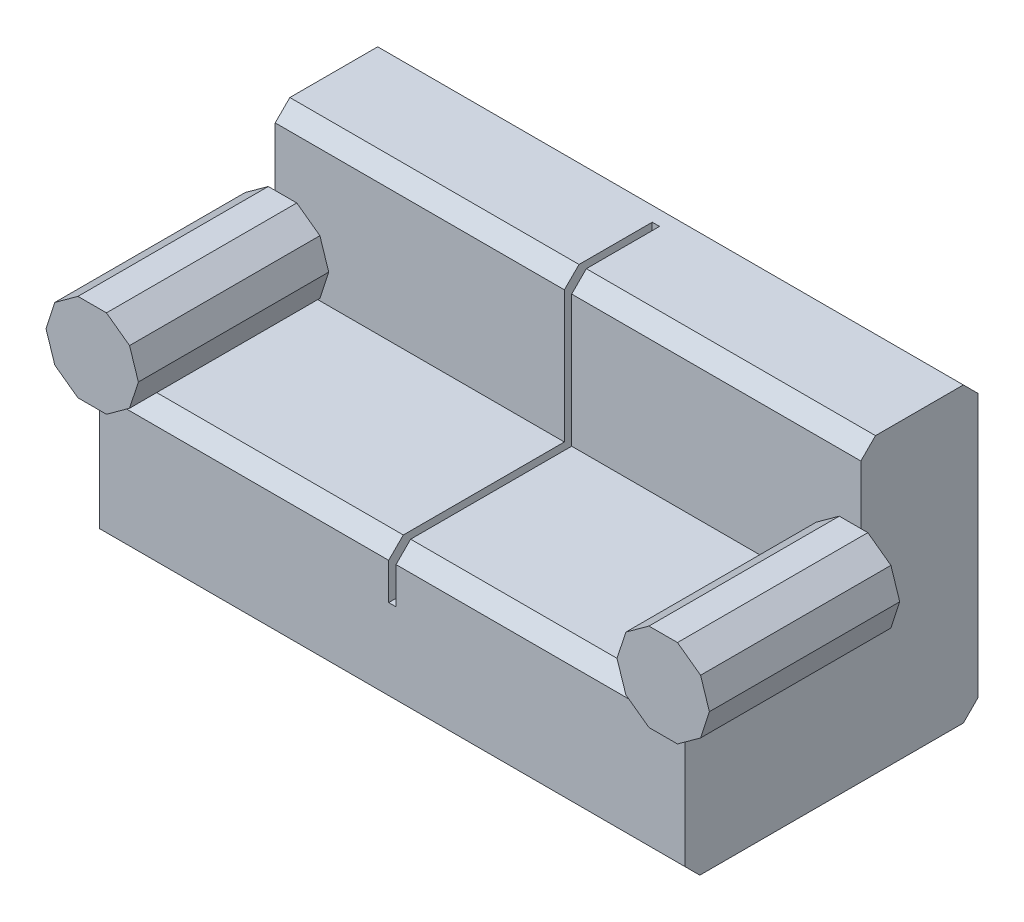
SolidWorks part; units mm, degrees
ref_plane "Front Plane" through (0, 0, 0) normal (0, 0, 1) x (1, 0, 0)
ref_plane "Top Plane" through (0, 0, 0) normal (0, 1, 0) x (1, 0, 0)
ref_plane "Right Plane" through (0, 0, 0) normal (1, 0, 0) x (0, 0, -1)
sketch "Sketch1" plane through (0, 0, 0) normal (1, 0, 0) x (0, 0, -1)
  line L0 (0, 0) -> (-55, 0)
  line L1 (-60, -5) -> (-60, -45)
  line L2 (-55, -50) -> (35, -50)
  line L3 (40, -45) -> (40, 45)
  line L4 (35, 50) -> (5, 50)
  line L5 (0, 45) -> (0, 0)
  line L6 (-55, 0) -> (-60, -5)
  line L7 (5, 50) -> (0, 45)
  line L8 (40, 45) -> (35, 50)
  line L9 (-60, -45) -> (-55, -50)
  line L10 (35, -50) -> (40, -45)
  point P1 (-60, 0)
  point P3 (-60, -50)
  point P4 (40, -50)
  point P5 (40, 50)
  point P6 (0, 50)
  point P17 (40, 0)
  dimension "D1" = 100
  dimension "D2" = 100
  dimension "D8" = 30
extrude "Boss-Extrude1" add sketch "Sketch1" along normal mid plane 200
sketch "Sketch2" plane through (0, 0, 0) normal (0, 0, 1) x (1, 0, 0)
  line L0 (100, 45) -> (100, 0) construction
  line L1 (113.2719, 10) -> (110.2598, 19.2705)
  line L2 (110.2598, 19.2705) -> (102.3738, 25)
  line L3 (102.3738, 25) -> (92.6262, 25)
  line L4 (92.6262, 25) -> (84.7402, 19.2705)
  line L5 (84.7402, 19.2705) -> (81.7281, 10)
  line L6 (81.7281, 10) -> (84.7402, 0.7295)
  line L7 (84.7402, 0.7295) -> (92.6262, -5)
  line L8 (92.6262, -5) -> (102.3738, -5)
  line L9 (102.3738, -5) -> (110.2598, 0.7295)
  line L10 (110.2598, 0.7295) -> (113.2719, 10)
  circle A0 centre (97.5, 10) radius 15 construction
  point P1 (88.7693, 5.2217)
  point P16 (90, 10)
  point P17 (0, 0)
  line M2 (-100, 0) -> (100, 0)
  line M3 (100, 0) -> (100, 45)
  dimension "D2" = 30
  dimension "D1" = 2.5
  dimension "D3" = 10
extrude "Boss-Extrude3" add sketch "Sketch2" along normal offset from surface (65 mm away) 5 contours L5 L6 L2 L3 L4 M2 M3 | L9 L10 L1 L2 L6 L7 L8 M3 M2 up to face at (0, -25, 60) offset beyond the face yes
mirror "Mirror1" about plane through (0, 0, 0) normal (1, 0, 0) of "Boss-Extrude3"
sketch "Sketch5" plane through (0, 0, 0) normal (0, 0, 1) x (1, 0, 0)
  line L0 (-1.25, 0) -> (-1.25, 50)
  line L1 (85.7443, 0) -> (-85.7443, 0) construction
  line L2 (100, 50) -> (-100, 50) construction
  line L3 (-1.25, 50) -> (1.25, 50)
  line L4 (1.25, 50) -> (1.25, 0)
  line L5 (1.25, 0) -> (-1.25, 0)
  point P7 (0, 50)
  dimension "D1" = 2.5
extrude "Cut-Extrude1" cut sketch "Sketch5" against normal blind 10
sketch "Sketch6" plane through (0, 50, 0) normal (0, 1, 0) x (1, 0, 0)
  line L0 (1.25, -60) -> (-1.25, -60)
  line L1 (-1.25, -60) -> (-1.25, 30)
  line L3 (1.25, 30) -> (1.25, -60)
  line L5 (1.25, 10) -> (1.25, 0) construction
  line L6 (92.6262, -60) -> (-92.6262, -60) construction
  line L7 (-1.25, 10) -> (-1.25, 5) construction
  line L8 (-1.25, 30) -> (1.25, 30)
  line L9 (100, 35) -> (-100, 35) construction
  point P3 (0, 30.5593)
  point P8 (0, 0)
  point P13 (0, 0)
  point P14 (0, 0)
  dimension "D1" = 5
extrude "Cut-Extrude3" cut sketch "Sketch6" against normal blind 5
sketch "Sketch7" plane through (0, 0, 0) normal (0, 1, 0) x (1, 0, 0)
  line L0 (-1.25, 10) -> (-1.25, -60)
  line L1 (92.6262, -60) -> (-92.6262, -60) construction
  line L2 (-1.25, -60) -> (1.25, -60)
  line L3 (1.25, -60) -> (1.25, 10)
  line L4 (1.25, 10) -> (-1.25, 10)
extrude "Cut-Extrude4" cut sketch "Sketch7" against normal blind 10
sketch "Sketch8" plane through (0, 0, 60) normal (0, 0, 1) x (1, 0, 0)
  line L0 (-1.25, 0) -> (-1.25, -17.5)
  line L1 (-1.25, 0) -> (-85.7443, 0) construction
  line L2 (-1.25, -5) -> (-1.25, 0) construction
  line L3 (-1.25, -17.5) -> (1.25, -17.5)
  line L4 (1.25, -17.5) -> (1.25, 0)
  line L5 (85.7443, 0) -> (1.25, 0) construction
  line L6 (1.25, 0) -> (-1.25, 0)
  line L7 (1.25, -10) -> (1.25, 45) construction
  line L8 (1.25, -10) -> (-1.25, -10) construction
  dimension "D1" = 7.5
extrude "Cut-Extrude5" cut sketch "Sketch8" against normal blind 5
